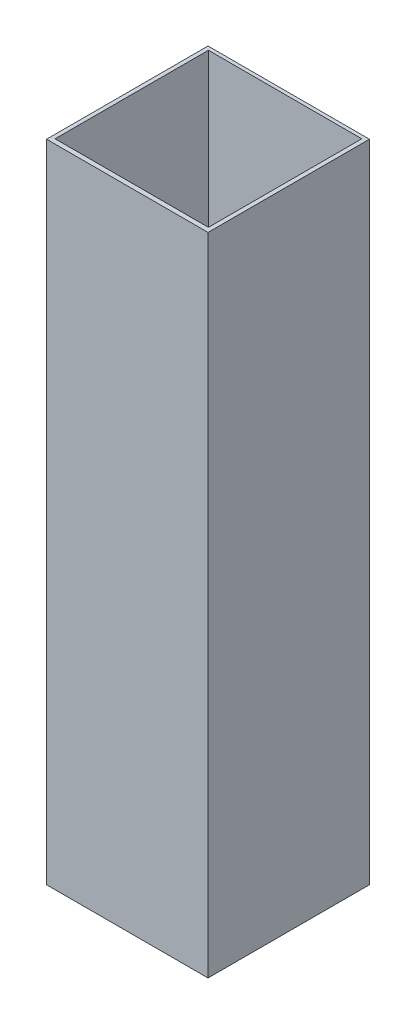
SolidWorks part; units mm, degrees
material "6061 Alloy"
ref_plane "Front Plane" through (0, 0, 0) normal (0, 0, 1) x (1, 0, 0)
ref_plane "Top Plane" through (0, 0, 0) normal (0, 1, 0) x (1, 0, 0)
ref_plane "Right Plane" through (0, 0, 0) normal (1, 0, 0) x (0, 0, -1)
sketch "Sketch1" plane through (0, 0, 0) normal (0, 1, 0) x (1, 0, 0)
  line L1 (-34.3833, 25.3569) -> (25.9417, 25.3569)
  line L2 (-34.3833, 25.3569) -> (-34.3833, -34.9681)
  line L3 (-34.3833, -34.9681) -> (25.9417, -34.9681)
  line L4 (25.9417, 25.3569) -> (25.9417, -34.9681)
  line L5 (-35.9137, 26.7183) -> (27.5863, 26.7183)
  line L6 (-35.9137, 26.7183) -> (-35.9137, -36.7817)
  line L7 (-35.9137, -36.7817) -> (27.5863, -36.7817)
  line L8 (27.5863, 26.7183) -> (27.5863, -36.7817)
  dimension "D1" = 60.325
  dimension "1.95" = 60.325
  dimension "2.05" = 63.5
  dimension "D2" = 63.5
extrude "Boss-Extrude1" add sketch "Sketch1" along normal blind 254
ref_plane "Plane1" through (0, 152.4, 0) normal (0, 1, 0) x (1, 0, 0)
sketch "Sketch3" plane through (0, 152.4, 0) normal (0, 1, 0) x (1, 0, 0)
  line L1 (-34.3833, 25.3569) -> (25.9417, 25.3569)
  line L2 (-34.3833, 25.3569) -> (-34.3833, -34.9681)
  line L3 (-34.3833, -34.9681) -> (25.9417, -34.9681)
  line L4 (25.9417, 25.3569) -> (25.9417, -34.9681)
extrude "Boss-Extrude3" add sketch "Sketch3" against normal blind 2.54
equation "\"1.95@Sketch1\"=2.5-(1/8)"
equation "\"D1@Sketch1\"=\"1.95@Sketch1\""
